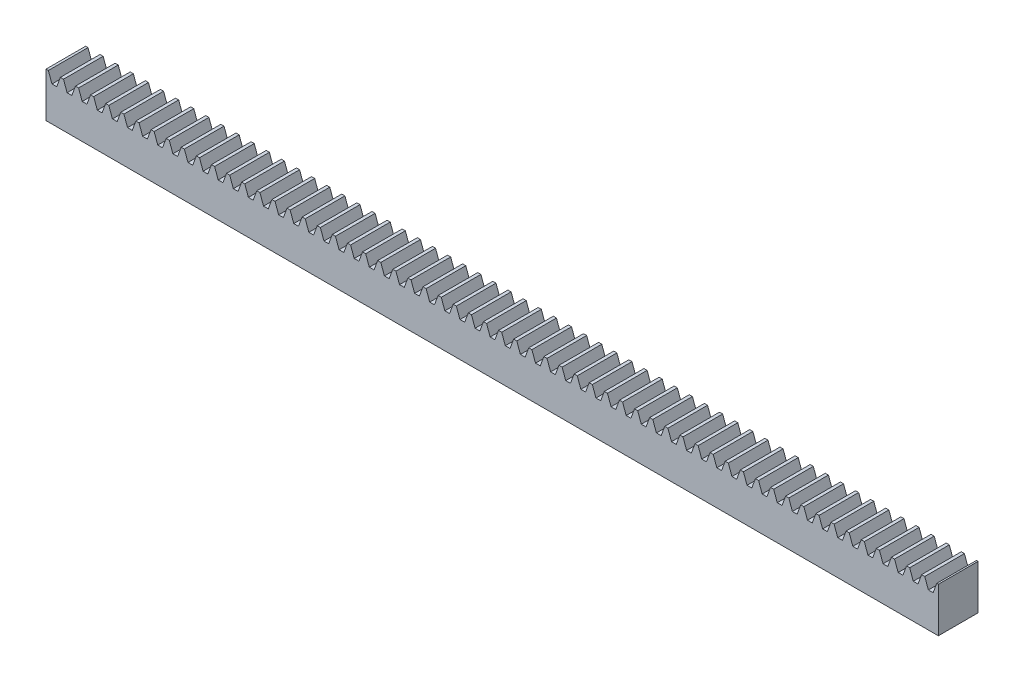
SolidWorks part; units mm, degrees
material "Nylon 101"
ref_plane "Front Plane" through (0, 0, 0) normal (0, 0, 1) x (1, 0, 0)
ref_plane "Top Plane" through (0, 0, 0) normal (0, 1, 0) x (1, 0, 0)
ref_plane "Right Plane" through (0, 0, 0) normal (1, 0, 0) x (0, 0, -1)
sketch "Sketch1" plane through (0, 0, 0) normal (0, 1, 0) x (1, 0, 0)
  line L0 (0, 0) -> (0, 4)
  line L1 (0, 4) -> (90, 4)
  line L2 (90, 4) -> (90, 0)
  line L3 (90, 0) -> (0, 0)
  dimension "D1" = 4
  dimension "D2" = 90
extrude "Boss-Extrude1" add sketch "Sketch1" along normal blind 4.5
sketch "Sketch2" plane through (0, 0, 0) normal (0, 0, 1) x (1, 0, 0)
  line L0 (0, 4) -> (90, 4) construction
  line L1 (0, 4.5) -> (0, 0) construction
  line L2 (90, 4.5) -> (90, 0) construction
  line L3 (0, 3.5) -> (90, 3.5) construction
  line L4 (0, 4.5) -> (90, 4.5) construction
  line L5 (0, 4.5) -> (0.239, 4.5) construction
  line L6 (0.239, 4.5) -> (0.603, 3.5)
  line L7 (0.603, 3.5) -> (0.842, 3.5)
  line L8 (1.081, 3.5) -> (1.445, 4.5)
  line L9 (1.445, 4.5) -> (1.684, 4.5) construction
  line L10 (0.842, 3.5) -> (1.081, 3.5)
  line L11 (0.239, 4.5) -> (1.445, 4.5)
  line L12 (1.763, 4.5) -> (2.127, 3.5)
  line L13 (2.127, 3.5) -> (2.366, 3.5)
  line L14 (2.605, 3.5) -> (2.969, 4.5)
  line L15 (2.366, 3.5) -> (2.605, 3.5)
  line L16 (1.763, 4.5) -> (2.969, 4.5)
  line L17 (1.524, 4.5) -> (1.763, 4.5) construction
  line L18 (2.969, 4.5) -> (3.208, 4.5) construction
  line L19 (3.287, 4.5) -> (3.651, 3.5)
  line L20 (3.651, 3.5) -> (3.89, 3.5)
  line L21 (4.129, 3.5) -> (4.493, 4.5)
  line L22 (3.89, 3.5) -> (4.129, 3.5)
  line L23 (3.287, 4.5) -> (4.493, 4.5)
  line L24 (3.048, 4.5) -> (3.287, 4.5) construction
  line L25 (4.493, 4.5) -> (4.732, 4.5) construction
  line L26 (4.811, 4.5) -> (5.175, 3.5)
  line L27 (5.175, 3.5) -> (5.414, 3.5)
  line L28 (5.653, 3.5) -> (6.017, 4.5)
  line L29 (5.414, 3.5) -> (5.653, 3.5)
  line L30 (4.811, 4.5) -> (6.017, 4.5)
  line L31 (4.572, 4.5) -> (4.811, 4.5) construction
  line L32 (6.017, 4.5) -> (6.256, 4.5) construction
  line L33 (6.335, 4.5) -> (6.699, 3.5)
  line L34 (6.699, 3.5) -> (6.938, 3.5)
  line L35 (7.177, 3.5) -> (7.541, 4.5)
  line L36 (6.938, 3.5) -> (7.177, 3.5)
  line L37 (6.335, 4.5) -> (7.541, 4.5)
  line L38 (6.096, 4.5) -> (6.335, 4.5) construction
  line L39 (7.541, 4.5) -> (7.78, 4.5) construction
  line L40 (7.859, 4.5) -> (8.223, 3.5)
  line L41 (8.223, 3.5) -> (8.462, 3.5)
  line L42 (8.701, 3.5) -> (9.065, 4.5)
  line L43 (8.462, 3.5) -> (8.701, 3.5)
  line L44 (7.859, 4.5) -> (9.065, 4.5)
  line L45 (7.62, 4.5) -> (7.859, 4.5) construction
  line L46 (9.065, 4.5) -> (9.304, 4.5) construction
  line L47 (9.383, 4.5) -> (9.747, 3.5)
  line L48 (9.747, 3.5) -> (9.986, 3.5)
  line L49 (10.225, 3.5) -> (10.589, 4.5)
  line L50 (9.986, 3.5) -> (10.225, 3.5)
  line L51 (9.383, 4.5) -> (10.589, 4.5)
  line L52 (9.144, 4.5) -> (9.383, 4.5) construction
  line L53 (10.589, 4.5) -> (10.828, 4.5) construction
  line L54 (10.907, 4.5) -> (11.271, 3.5)
  line L55 (11.271, 3.5) -> (11.51, 3.5)
  line L56 (11.749, 3.5) -> (12.113, 4.5)
  line L57 (11.51, 3.5) -> (11.749, 3.5)
  line L58 (10.907, 4.5) -> (12.113, 4.5)
  line L59 (10.668, 4.5) -> (10.907, 4.5) construction
  line L60 (12.113, 4.5) -> (12.352, 4.5) construction
  line L61 (12.431, 4.5) -> (12.795, 3.5)
  line L62 (12.795, 3.5) -> (13.034, 3.5)
  line L63 (13.273, 3.5) -> (13.637, 4.5)
  line L64 (13.034, 3.5) -> (13.273, 3.5)
  line L65 (12.431, 4.5) -> (13.637, 4.5)
  line L66 (12.192, 4.5) -> (12.431, 4.5) construction
  line L67 (13.637, 4.5) -> (13.876, 4.5) construction
  line L68 (13.955, 4.5) -> (14.319, 3.5)
  line L69 (14.319, 3.5) -> (14.558, 3.5)
  line L70 (14.797, 3.5) -> (15.161, 4.5)
  line L71 (14.558, 3.5) -> (14.797, 3.5)
  line L72 (13.955, 4.5) -> (15.161, 4.5)
  line L73 (13.716, 4.5) -> (13.955, 4.5) construction
  line L74 (15.161, 4.5) -> (15.4, 4.5) construction
  line L75 (15.479, 4.5) -> (15.843, 3.5)
  line L76 (15.843, 3.5) -> (16.082, 3.5)
  line L77 (16.321, 3.5) -> (16.685, 4.5)
  line L78 (16.082, 3.5) -> (16.321, 3.5)
  line L79 (15.479, 4.5) -> (16.685, 4.5)
  line L80 (15.24, 4.5) -> (15.479, 4.5) construction
  line L81 (16.685, 4.5) -> (16.924, 4.5) construction
  line L82 (17.003, 4.5) -> (17.367, 3.5)
  line L83 (17.367, 3.5) -> (17.606, 3.5)
  line L84 (17.845, 3.5) -> (18.209, 4.5)
  line L85 (17.606, 3.5) -> (17.845, 3.5)
  line L86 (17.003, 4.5) -> (18.209, 4.5)
  line L87 (16.764, 4.5) -> (17.003, 4.5) construction
  line L88 (18.209, 4.5) -> (18.448, 4.5) construction
  line L89 (18.527, 4.5) -> (18.891, 3.5)
  line L90 (18.891, 3.5) -> (19.13, 3.5)
  line L91 (19.369, 3.5) -> (19.733, 4.5)
  line L92 (19.13, 3.5) -> (19.369, 3.5)
  line L93 (18.527, 4.5) -> (19.733, 4.5)
  line L94 (18.288, 4.5) -> (18.527, 4.5) construction
  line L95 (19.733, 4.5) -> (19.972, 4.5) construction
  line L96 (20.051, 4.5) -> (20.415, 3.5)
  line L97 (20.415, 3.5) -> (20.654, 3.5)
  line L98 (20.893, 3.5) -> (21.257, 4.5)
  line L99 (20.654, 3.5) -> (20.893, 3.5)
  line L100 (20.051, 4.5) -> (21.257, 4.5)
  line L101 (19.812, 4.5) -> (20.051, 4.5) construction
  line L102 (21.257, 4.5) -> (21.496, 4.5) construction
  line L103 (21.575, 4.5) -> (21.939, 3.5)
  line L104 (21.939, 3.5) -> (22.178, 3.5)
  line L105 (22.417, 3.5) -> (22.781, 4.5)
  line L106 (22.178, 3.5) -> (22.417, 3.5)
  line L107 (21.575, 4.5) -> (22.781, 4.5)
  line L108 (21.336, 4.5) -> (21.575, 4.5) construction
  line L109 (22.781, 4.5) -> (23.02, 4.5) construction
  line L110 (23.099, 4.5) -> (23.463, 3.5)
  line L111 (23.463, 3.5) -> (23.702, 3.5)
  line L112 (23.941, 3.5) -> (24.305, 4.5)
  line L113 (23.702, 3.5) -> (23.941, 3.5)
  line L114 (23.099, 4.5) -> (24.305, 4.5)
  line L115 (22.86, 4.5) -> (23.099, 4.5) construction
  line L116 (24.305, 4.5) -> (24.544, 4.5) construction
  line L117 (24.623, 4.5) -> (24.987, 3.5)
  line L118 (24.987, 3.5) -> (25.226, 3.5)
  line L119 (25.465, 3.5) -> (25.829, 4.5)
  line L120 (25.226, 3.5) -> (25.465, 3.5)
  line L121 (24.623, 4.5) -> (25.829, 4.5)
  line L122 (24.384, 4.5) -> (24.623, 4.5) construction
  line L123 (25.829, 4.5) -> (26.068, 4.5) construction
  line L124 (26.147, 4.5) -> (26.511, 3.5)
  line L125 (26.511, 3.5) -> (26.75, 3.5)
  line L126 (26.989, 3.5) -> (27.353, 4.5)
  line L127 (26.75, 3.5) -> (26.989, 3.5)
  line L128 (26.147, 4.5) -> (27.353, 4.5)
  line L129 (25.908, 4.5) -> (26.147, 4.5) construction
  line L130 (27.353, 4.5) -> (27.592, 4.5) construction
  line L131 (27.671, 4.5) -> (28.035, 3.5)
  line L132 (28.035, 3.5) -> (28.274, 3.5)
  line L133 (28.513, 3.5) -> (28.877, 4.5)
  line L134 (28.274, 3.5) -> (28.513, 3.5)
  line L135 (27.671, 4.5) -> (28.877, 4.5)
  line L136 (27.432, 4.5) -> (27.671, 4.5) construction
  line L137 (28.877, 4.5) -> (29.116, 4.5) construction
  line L138 (29.195, 4.5) -> (29.559, 3.5)
  line L139 (29.559, 3.5) -> (29.798, 3.5)
  line L140 (30.037, 3.5) -> (30.401, 4.5)
  line L141 (29.798, 3.5) -> (30.037, 3.5)
  line L142 (29.195, 4.5) -> (30.401, 4.5)
  line L143 (28.956, 4.5) -> (29.195, 4.5) construction
  line L144 (30.401, 4.5) -> (30.64, 4.5) construction
  line L145 (30.719, 4.5) -> (31.083, 3.5)
  line L146 (31.083, 3.5) -> (31.322, 3.5)
  line L147 (31.561, 3.5) -> (31.925, 4.5)
  line L148 (31.322, 3.5) -> (31.561, 3.5)
  line L149 (30.719, 4.5) -> (31.925, 4.5)
  line L150 (30.48, 4.5) -> (30.719, 4.5) construction
  line L151 (31.925, 4.5) -> (32.164, 4.5) construction
  line L152 (32.243, 4.5) -> (32.607, 3.5)
  line L153 (32.607, 3.5) -> (32.846, 3.5)
  line L154 (33.085, 3.5) -> (33.449, 4.5)
  line L155 (32.846, 3.5) -> (33.085, 3.5)
  line L156 (32.243, 4.5) -> (33.449, 4.5)
  line L157 (32.004, 4.5) -> (32.243, 4.5) construction
  line L158 (33.449, 4.5) -> (33.688, 4.5) construction
  line L159 (33.767, 4.5) -> (34.131, 3.5)
  line L160 (34.131, 3.5) -> (34.37, 3.5)
  line L161 (34.609, 3.5) -> (34.973, 4.5)
  line L162 (34.37, 3.5) -> (34.609, 3.5)
  line L163 (33.767, 4.5) -> (34.973, 4.5)
  line L164 (33.528, 4.5) -> (33.767, 4.5) construction
  line L165 (34.973, 4.5) -> (35.212, 4.5) construction
  line L166 (35.291, 4.5) -> (35.655, 3.5)
  line L167 (35.655, 3.5) -> (35.894, 3.5)
  line L168 (36.133, 3.5) -> (36.497, 4.5)
  line L169 (35.894, 3.5) -> (36.133, 3.5)
  line L170 (35.291, 4.5) -> (36.497, 4.5)
  line L171 (35.052, 4.5) -> (35.291, 4.5) construction
  line L172 (36.497, 4.5) -> (36.736, 4.5) construction
  line L173 (36.815, 4.5) -> (37.179, 3.5)
  line L174 (37.179, 3.5) -> (37.418, 3.5)
  line L175 (37.657, 3.5) -> (38.021, 4.5)
  line L176 (37.418, 3.5) -> (37.657, 3.5)
  line L177 (36.815, 4.5) -> (38.021, 4.5)
  line L178 (36.576, 4.5) -> (36.815, 4.5) construction
  line L179 (38.021, 4.5) -> (38.26, 4.5) construction
  line L180 (38.339, 4.5) -> (38.703, 3.5)
  line L181 (38.703, 3.5) -> (38.942, 3.5)
  line L182 (39.181, 3.5) -> (39.545, 4.5)
  line L183 (38.942, 3.5) -> (39.181, 3.5)
  line L184 (38.339, 4.5) -> (39.545, 4.5)
  line L185 (38.1, 4.5) -> (38.339, 4.5) construction
  line L186 (39.545, 4.5) -> (39.784, 4.5) construction
  line L187 (39.863, 4.5) -> (40.227, 3.5)
  line L188 (40.227, 3.5) -> (40.466, 3.5)
  line L189 (40.705, 3.5) -> (41.069, 4.5)
  line L190 (40.466, 3.5) -> (40.705, 3.5)
  line L191 (39.863, 4.5) -> (41.069, 4.5)
  line L192 (39.624, 4.5) -> (39.863, 4.5) construction
  line L193 (41.069, 4.5) -> (41.308, 4.5) construction
  line L194 (41.387, 4.5) -> (41.751, 3.5)
  line L195 (41.751, 3.5) -> (41.99, 3.5)
  line L196 (42.229, 3.5) -> (42.593, 4.5)
  line L197 (41.99, 3.5) -> (42.229, 3.5)
  line L198 (41.387, 4.5) -> (42.593, 4.5)
  line L199 (41.148, 4.5) -> (41.387, 4.5) construction
  line L200 (42.593, 4.5) -> (42.832, 4.5) construction
  line L201 (42.911, 4.5) -> (43.275, 3.5)
  line L202 (43.275, 3.5) -> (43.514, 3.5)
  line L203 (43.753, 3.5) -> (44.117, 4.5)
  line L204 (43.514, 3.5) -> (43.753, 3.5)
  line L205 (42.911, 4.5) -> (44.117, 4.5)
  line L206 (42.672, 4.5) -> (42.911, 4.5) construction
  line L207 (44.117, 4.5) -> (44.356, 4.5) construction
  line L208 (44.435, 4.5) -> (44.799, 3.5)
  line L209 (44.799, 3.5) -> (45.038, 3.5)
  line L210 (45.277, 3.5) -> (45.641, 4.5)
  line L211 (45.038, 3.5) -> (45.277, 3.5)
  line L212 (44.435, 4.5) -> (45.641, 4.5)
  line L213 (44.196, 4.5) -> (44.435, 4.5) construction
  line L214 (45.641, 4.5) -> (45.88, 4.5) construction
  line L215 (45.959, 4.5) -> (46.323, 3.5)
  line L216 (46.323, 3.5) -> (46.562, 3.5)
  line L217 (46.801, 3.5) -> (47.165, 4.5)
  line L218 (46.562, 3.5) -> (46.801, 3.5)
  line L219 (45.959, 4.5) -> (47.165, 4.5)
  line L220 (45.72, 4.5) -> (45.959, 4.5) construction
  line L221 (47.165, 4.5) -> (47.404, 4.5) construction
  line L222 (47.483, 4.5) -> (47.847, 3.5)
  line L223 (47.847, 3.5) -> (48.086, 3.5)
  line L224 (48.325, 3.5) -> (48.689, 4.5)
  line L225 (48.086, 3.5) -> (48.325, 3.5)
  line L226 (47.483, 4.5) -> (48.689, 4.5)
  line L227 (47.244, 4.5) -> (47.483, 4.5) construction
  line L228 (48.689, 4.5) -> (48.928, 4.5) construction
  line L229 (49.007, 4.5) -> (49.371, 3.5)
  line L230 (49.371, 3.5) -> (49.61, 3.5)
  line L231 (49.849, 3.5) -> (50.213, 4.5)
  line L232 (49.61, 3.5) -> (49.849, 3.5)
  line L233 (49.007, 4.5) -> (50.213, 4.5)
  line L234 (48.768, 4.5) -> (49.007, 4.5) construction
  line L235 (50.213, 4.5) -> (50.452, 4.5) construction
  line L236 (50.531, 4.5) -> (50.895, 3.5)
  line L237 (50.895, 3.5) -> (51.134, 3.5)
  line L238 (51.373, 3.5) -> (51.737, 4.5)
  line L239 (51.134, 3.5) -> (51.373, 3.5)
  line L240 (50.531, 4.5) -> (51.737, 4.5)
  line L241 (50.292, 4.5) -> (50.531, 4.5) construction
  line L242 (51.737, 4.5) -> (51.976, 4.5) construction
  line L243 (52.055, 4.5) -> (52.419, 3.5)
  line L244 (52.419, 3.5) -> (52.658, 3.5)
  line L245 (52.897, 3.5) -> (53.261, 4.5)
  line L246 (52.658, 3.5) -> (52.897, 3.5)
  line L247 (52.055, 4.5) -> (53.261, 4.5)
  line L248 (51.816, 4.5) -> (52.055, 4.5) construction
  line L249 (53.261, 4.5) -> (53.5, 4.5) construction
  line L250 (53.579, 4.5) -> (53.943, 3.5)
  line L251 (53.943, 3.5) -> (54.182, 3.5)
  line L252 (54.421, 3.5) -> (54.785, 4.5)
  line L253 (54.182, 3.5) -> (54.421, 3.5)
  line L254 (53.579, 4.5) -> (54.785, 4.5)
  line L255 (53.34, 4.5) -> (53.579, 4.5) construction
  line L256 (54.785, 4.5) -> (55.024, 4.5) construction
  line L257 (55.103, 4.5) -> (55.467, 3.5)
  line L258 (55.467, 3.5) -> (55.706, 3.5)
  line L259 (55.945, 3.5) -> (56.309, 4.5)
  line L260 (55.706, 3.5) -> (55.945, 3.5)
  line L261 (55.103, 4.5) -> (56.309, 4.5)
  line L262 (54.864, 4.5) -> (55.103, 4.5) construction
  line L263 (56.309, 4.5) -> (56.548, 4.5) construction
  line L264 (56.627, 4.5) -> (56.991, 3.5)
  line L265 (56.991, 3.5) -> (57.23, 3.5)
  line L266 (57.469, 3.5) -> (57.833, 4.5)
  line L267 (57.23, 3.5) -> (57.469, 3.5)
  line L268 (56.627, 4.5) -> (57.833, 4.5)
  line L269 (56.388, 4.5) -> (56.627, 4.5) construction
  line L270 (57.833, 4.5) -> (58.072, 4.5) construction
  line L271 (58.151, 4.5) -> (58.515, 3.5)
  line L272 (58.515, 3.5) -> (58.754, 3.5)
  line L273 (58.993, 3.5) -> (59.357, 4.5)
  line L274 (58.754, 3.5) -> (58.993, 3.5)
  line L275 (58.151, 4.5) -> (59.357, 4.5)
  line L276 (57.912, 4.5) -> (58.151, 4.5) construction
  line L277 (59.357, 4.5) -> (59.596, 4.5) construction
  line L278 (59.675, 4.5) -> (60.039, 3.5)
  line L279 (60.039, 3.5) -> (60.278, 3.5)
  line L280 (60.517, 3.5) -> (60.881, 4.5)
  line L281 (60.278, 3.5) -> (60.517, 3.5)
  line L282 (59.675, 4.5) -> (60.881, 4.5)
  line L283 (59.436, 4.5) -> (59.675, 4.5) construction
  line L284 (60.881, 4.5) -> (61.12, 4.5) construction
  line L285 (61.199, 4.5) -> (61.563, 3.5)
  line L286 (61.563, 3.5) -> (61.802, 3.5)
  line L287 (62.041, 3.5) -> (62.405, 4.5)
  line L288 (61.802, 3.5) -> (62.041, 3.5)
  line L289 (61.199, 4.5) -> (62.405, 4.5)
  line L290 (60.96, 4.5) -> (61.199, 4.5) construction
  line L291 (62.405, 4.5) -> (62.644, 4.5) construction
  line L292 (62.723, 4.5) -> (63.087, 3.5)
  line L293 (63.087, 3.5) -> (63.326, 3.5)
  line L294 (63.565, 3.5) -> (63.929, 4.5)
  line L295 (63.326, 3.5) -> (63.565, 3.5)
  line L296 (62.723, 4.5) -> (63.929, 4.5)
  line L297 (62.484, 4.5) -> (62.723, 4.5) construction
  line L298 (63.929, 4.5) -> (64.168, 4.5) construction
  line L299 (64.247, 4.5) -> (64.611, 3.5)
  line L300 (64.611, 3.5) -> (64.85, 3.5)
  line L301 (65.089, 3.5) -> (65.453, 4.5)
  line L302 (64.85, 3.5) -> (65.089, 3.5)
  line L303 (64.247, 4.5) -> (65.453, 4.5)
  line L304 (64.008, 4.5) -> (64.247, 4.5) construction
  line L305 (65.453, 4.5) -> (65.692, 4.5) construction
  line L306 (65.771, 4.5) -> (66.135, 3.5)
  line L307 (66.135, 3.5) -> (66.374, 3.5)
  line L308 (66.613, 3.5) -> (66.977, 4.5)
  line L309 (66.374, 3.5) -> (66.613, 3.5)
  line L310 (65.771, 4.5) -> (66.977, 4.5)
  line L311 (65.532, 4.5) -> (65.771, 4.5) construction
  line L312 (66.977, 4.5) -> (67.216, 4.5) construction
  line L313 (67.295, 4.5) -> (67.659, 3.5)
  line L314 (67.659, 3.5) -> (67.898, 3.5)
  line L315 (68.137, 3.5) -> (68.501, 4.5)
  line L316 (67.898, 3.5) -> (68.137, 3.5)
  line L317 (67.295, 4.5) -> (68.501, 4.5)
  line L318 (67.056, 4.5) -> (67.295, 4.5) construction
  line L319 (68.501, 4.5) -> (68.74, 4.5) construction
  line L320 (68.819, 4.5) -> (69.183, 3.5)
  line L321 (69.183, 3.5) -> (69.422, 3.5)
  line L322 (69.661, 3.5) -> (70.025, 4.5)
  line L323 (69.422, 3.5) -> (69.661, 3.5)
  line L324 (68.819, 4.5) -> (70.025, 4.5)
  line L325 (68.58, 4.5) -> (68.819, 4.5) construction
  line L326 (70.025, 4.5) -> (70.264, 4.5) construction
  line L327 (70.343, 4.5) -> (70.707, 3.5)
  line L328 (70.707, 3.5) -> (70.946, 3.5)
  line L329 (71.185, 3.5) -> (71.549, 4.5)
  line L330 (70.946, 3.5) -> (71.185, 3.5)
  line L331 (70.343, 4.5) -> (71.549, 4.5)
  line L332 (70.104, 4.5) -> (70.343, 4.5) construction
  line L333 (71.549, 4.5) -> (71.788, 4.5) construction
  line L334 (71.867, 4.5) -> (72.231, 3.5)
  line L335 (72.231, 3.5) -> (72.47, 3.5)
  line L336 (72.709, 3.5) -> (73.073, 4.5)
  line L337 (72.47, 3.5) -> (72.709, 3.5)
  line L338 (71.867, 4.5) -> (73.073, 4.5)
  line L339 (71.628, 4.5) -> (71.867, 4.5) construction
  line L340 (73.073, 4.5) -> (73.312, 4.5) construction
  line L341 (73.391, 4.5) -> (73.755, 3.5)
  line L342 (73.755, 3.5) -> (73.994, 3.5)
  line L343 (74.233, 3.5) -> (74.597, 4.5)
  line L344 (73.994, 3.5) -> (74.233, 3.5)
  line L345 (73.391, 4.5) -> (74.597, 4.5)
  line L346 (73.152, 4.5) -> (73.391, 4.5) construction
  line L347 (74.597, 4.5) -> (74.836, 4.5) construction
  line L348 (74.915, 4.5) -> (75.279, 3.5)
  line L349 (75.279, 3.5) -> (75.518, 3.5)
  line L350 (75.757, 3.5) -> (76.121, 4.5)
  line L351 (75.518, 3.5) -> (75.757, 3.5)
  line L352 (74.915, 4.5) -> (76.121, 4.5)
  line L353 (74.676, 4.5) -> (74.915, 4.5) construction
  line L354 (76.121, 4.5) -> (76.36, 4.5) construction
  line L355 (76.439, 4.5) -> (76.803, 3.5)
  line L356 (76.803, 3.5) -> (77.042, 3.5)
  line L357 (77.281, 3.5) -> (77.645, 4.5)
  line L358 (77.042, 3.5) -> (77.281, 3.5)
  line L359 (76.439, 4.5) -> (77.645, 4.5)
  line L360 (76.2, 4.5) -> (76.439, 4.5) construction
  line L361 (77.645, 4.5) -> (77.884, 4.5) construction
  line L362 (77.963, 4.5) -> (78.327, 3.5)
  line L363 (78.327, 3.5) -> (78.566, 3.5)
  line L364 (78.805, 3.5) -> (79.169, 4.5)
  line L365 (78.566, 3.5) -> (78.805, 3.5)
  line L366 (77.963, 4.5) -> (79.169, 4.5)
  line L367 (77.724, 4.5) -> (77.963, 4.5) construction
  line L368 (79.169, 4.5) -> (79.408, 4.5) construction
  line L369 (79.487, 4.5) -> (79.851, 3.5)
  line L370 (79.851, 3.5) -> (80.09, 3.5)
  line L371 (80.329, 3.5) -> (80.693, 4.5)
  line L372 (80.09, 3.5) -> (80.329, 3.5)
  line L373 (79.487, 4.5) -> (80.693, 4.5)
  line L374 (79.248, 4.5) -> (79.487, 4.5) construction
  line L375 (80.693, 4.5) -> (80.932, 4.5) construction
  line L376 (81.011, 4.5) -> (81.375, 3.5)
  line L377 (81.375, 3.5) -> (81.614, 3.5)
  line L378 (81.853, 3.5) -> (82.217, 4.5)
  line L379 (81.614, 3.5) -> (81.853, 3.5)
  line L380 (81.011, 4.5) -> (82.217, 4.5)
  line L381 (80.772, 4.5) -> (81.011, 4.5) construction
  line L382 (82.217, 4.5) -> (82.456, 4.5) construction
  line L383 (82.535, 4.5) -> (82.899, 3.5)
  line L384 (82.899, 3.5) -> (83.138, 3.5)
  line L385 (83.377, 3.5) -> (83.741, 4.5)
  line L386 (83.138, 3.5) -> (83.377, 3.5)
  line L387 (82.535, 4.5) -> (83.741, 4.5)
  line L388 (82.296, 4.5) -> (82.535, 4.5) construction
  line L389 (83.741, 4.5) -> (83.98, 4.5) construction
  line L390 (84.059, 4.5) -> (84.423, 3.5)
  line L391 (84.423, 3.5) -> (84.662, 3.5)
  line L392 (84.901, 3.5) -> (85.265, 4.5)
  line L393 (84.662, 3.5) -> (84.901, 3.5)
  line L394 (84.059, 4.5) -> (85.265, 4.5)
  line L395 (83.82, 4.5) -> (84.059, 4.5) construction
  line L396 (85.265, 4.5) -> (85.504, 4.5) construction
  line L397 (85.583, 4.5) -> (85.947, 3.5)
  line L398 (85.947, 3.5) -> (86.186, 3.5)
  line L399 (86.425, 3.5) -> (86.789, 4.5)
  line L400 (86.186, 3.5) -> (86.425, 3.5)
  line L401 (85.583, 4.5) -> (86.789, 4.5)
  line L402 (85.344, 4.5) -> (85.583, 4.5) construction
  line L403 (86.789, 4.5) -> (87.028, 4.5) construction
  line L404 (87.107, 4.5) -> (87.471, 3.5)
  line L405 (87.471, 3.5) -> (87.71, 3.5)
  line L406 (87.949, 3.5) -> (88.313, 4.5)
  line L407 (87.71, 3.5) -> (87.949, 3.5)
  line L408 (87.107, 4.5) -> (88.313, 4.5)
  line L409 (86.868, 4.5) -> (87.107, 4.5) construction
  line L410 (88.313, 4.5) -> (88.552, 4.5) construction
  line L411 (88.631, 4.5) -> (88.995, 3.5)
  line L412 (88.995, 3.5) -> (89.234, 3.5)
  line L413 (89.473, 3.5) -> (89.837, 4.5)
  line L414 (89.234, 3.5) -> (89.473, 3.5)
  line L415 (88.631, 4.5) -> (89.837, 4.5)
  line L416 (88.392, 4.5) -> (88.631, 4.5) construction
  line L417 (89.837, 4.5) -> (90.076, 4.5) construction
  line L418 (90.155, 4.5) -> (90.519, 3.5)
  line L419 (90.519, 3.5) -> (90.758, 3.5)
  line L420 (90.997, 3.5) -> (91.361, 4.5)
  line L421 (90.758, 3.5) -> (90.997, 3.5)
  line L422 (90.155, 4.5) -> (91.361, 4.5)
  line L423 (89.916, 4.5) -> (90.155, 4.5) construction
  line L424 (91.361, 4.5) -> (91.6, 4.5) construction
  line L425 (91.679, 4.5) -> (92.043, 3.5)
  line L426 (92.043, 3.5) -> (92.282, 3.5)
  line L427 (92.521, 3.5) -> (92.885, 4.5)
  line L428 (92.282, 3.5) -> (92.521, 3.5)
  line L429 (91.679, 4.5) -> (92.885, 4.5)
  line L430 (91.44, 4.5) -> (91.679, 4.5) construction
  line L431 (92.885, 4.5) -> (93.124, 4.5) construction
  line L432 (93.203, 4.5) -> (93.567, 3.5)
  line L433 (93.567, 3.5) -> (93.806, 3.5)
  line L434 (94.045, 3.5) -> (94.409, 4.5)
  line L435 (93.806, 3.5) -> (94.045, 3.5)
  line L436 (93.203, 4.5) -> (94.409, 4.5)
  line L437 (92.964, 4.5) -> (93.203, 4.5) construction
  line L438 (94.409, 4.5) -> (94.648, 4.5) construction
  line L439 (94.727, 4.5) -> (95.091, 3.5)
  line L440 (95.091, 3.5) -> (95.33, 3.5)
  line L441 (95.569, 3.5) -> (95.933, 4.5)
  line L442 (95.33, 3.5) -> (95.569, 3.5)
  line L443 (94.727, 4.5) -> (95.933, 4.5)
  line L444 (94.488, 4.5) -> (94.727, 4.5) construction
  line L445 (95.933, 4.5) -> (96.172, 4.5) construction
  line L446 (96.251, 4.5) -> (96.615, 3.5)
  line L447 (96.615, 3.5) -> (96.854, 3.5)
  line L448 (97.093, 3.5) -> (97.457, 4.5)
  line L449 (96.854, 3.5) -> (97.093, 3.5)
  line L450 (96.251, 4.5) -> (97.457, 4.5)
  line L451 (96.012, 4.5) -> (96.251, 4.5) construction
  line L452 (97.457, 4.5) -> (97.696, 4.5) construction
  line L453 (97.775, 4.5) -> (98.139, 3.5)
  line L454 (98.139, 3.5) -> (98.378, 3.5)
  line L455 (98.617, 3.5) -> (98.981, 4.5)
  line L456 (98.378, 3.5) -> (98.617, 3.5)
  line L457 (97.775, 4.5) -> (98.981, 4.5)
  line L458 (97.536, 4.5) -> (97.775, 4.5) construction
  line L459 (98.981, 4.5) -> (99.22, 4.5) construction
  line L460 (99.299, 4.5) -> (99.663, 3.5)
  line L461 (99.663, 3.5) -> (99.902, 3.5)
  line L462 (100.141, 3.5) -> (100.505, 4.5)
  line L463 (99.902, 3.5) -> (100.141, 3.5)
  line L464 (99.299, 4.5) -> (100.505, 4.5)
  line L465 (99.06, 4.5) -> (99.299, 4.5) construction
  line L466 (100.505, 4.5) -> (100.744, 4.5) construction
  line L467 (100.823, 4.5) -> (101.187, 3.5)
  line L468 (101.187, 3.5) -> (101.426, 3.5)
  line L469 (101.665, 3.5) -> (102.029, 4.5)
  line L470 (101.426, 3.5) -> (101.665, 3.5)
  line L471 (100.823, 4.5) -> (102.029, 4.5)
  line L472 (100.584, 4.5) -> (100.823, 4.5) construction
  line L473 (102.029, 4.5) -> (102.268, 4.5) construction
  line L474 (102.347, 4.5) -> (102.711, 3.5)
  line L475 (102.711, 3.5) -> (102.95, 3.5)
  line L476 (103.189, 3.5) -> (103.553, 4.5)
  line L477 (102.95, 3.5) -> (103.189, 3.5)
  line L478 (102.347, 4.5) -> (103.553, 4.5)
  line L479 (102.108, 4.5) -> (102.347, 4.5) construction
  line L480 (103.553, 4.5) -> (103.792, 4.5) construction
  line L481 (103.871, 4.5) -> (104.235, 3.5)
  line L482 (104.235, 3.5) -> (104.474, 3.5)
  line L483 (104.713, 3.5) -> (105.077, 4.5)
  line L484 (104.474, 3.5) -> (104.713, 3.5)
  line L485 (103.871, 4.5) -> (105.077, 4.5)
  line L486 (103.632, 4.5) -> (103.871, 4.5) construction
  line L487 (105.077, 4.5) -> (105.316, 4.5) construction
  line L488 (105.395, 4.5) -> (105.759, 3.5)
  line L489 (105.759, 3.5) -> (105.998, 3.5)
  line L490 (106.237, 3.5) -> (106.601, 4.5)
  line L491 (105.998, 3.5) -> (106.237, 3.5)
  line L492 (105.395, 4.5) -> (106.601, 4.5)
  line L493 (105.156, 4.5) -> (105.395, 4.5) construction
  line L494 (106.601, 4.5) -> (106.84, 4.5) construction
  line L495 (106.919, 4.5) -> (107.283, 3.5)
  line L496 (107.283, 3.5) -> (107.522, 3.5)
  line L497 (107.761, 3.5) -> (108.125, 4.5)
  line L498 (107.522, 3.5) -> (107.761, 3.5)
  line L499 (106.919, 4.5) -> (108.125, 4.5)
  line L500 (106.68, 4.5) -> (106.919, 4.5) construction
  line L501 (108.125, 4.5) -> (108.364, 4.5) construction
  line L502 (108.443, 4.5) -> (108.807, 3.5)
  line L503 (108.807, 3.5) -> (109.046, 3.5)
  line L504 (109.285, 3.5) -> (109.649, 4.5)
  line L505 (109.046, 3.5) -> (109.285, 3.5)
  line L506 (108.443, 4.5) -> (109.649, 4.5)
  line L507 (108.204, 4.5) -> (108.443, 4.5) construction
  line L508 (109.649, 4.5) -> (109.888, 4.5) construction
  line L509 (109.967, 4.5) -> (110.331, 3.5)
  line L510 (110.331, 3.5) -> (110.57, 3.5)
  line L511 (110.809, 3.5) -> (111.173, 4.5)
  line L512 (110.57, 3.5) -> (110.809, 3.5)
  line L513 (109.967, 4.5) -> (111.173, 4.5)
  line L514 (109.728, 4.5) -> (109.967, 4.5) construction
  line L515 (111.173, 4.5) -> (111.412, 4.5) construction
  line L516 (111.491, 4.5) -> (111.855, 3.5)
  line L517 (111.855, 3.5) -> (112.094, 3.5)
  line L518 (112.333, 3.5) -> (112.697, 4.5)
  line L519 (112.094, 3.5) -> (112.333, 3.5)
  line L520 (111.491, 4.5) -> (112.697, 4.5)
  line L521 (111.252, 4.5) -> (111.491, 4.5) construction
  line L522 (112.697, 4.5) -> (112.936, 4.5) construction
  line L523 (113.015, 4.5) -> (113.379, 3.5)
  line L524 (113.379, 3.5) -> (113.618, 3.5)
  line L525 (113.857, 3.5) -> (114.221, 4.5)
  line L526 (113.618, 3.5) -> (113.857, 3.5)
  line L527 (113.015, 4.5) -> (114.221, 4.5)
  line L528 (112.776, 4.5) -> (113.015, 4.5) construction
  line L529 (114.221, 4.5) -> (114.46, 4.5) construction
  line L530 (114.539, 4.5) -> (114.903, 3.5)
  line L531 (114.903, 3.5) -> (115.142, 3.5)
  line L532 (115.381, 3.5) -> (115.745, 4.5)
  line L533 (115.142, 3.5) -> (115.381, 3.5)
  line L534 (114.539, 4.5) -> (115.745, 4.5)
  line L535 (114.3, 4.5) -> (114.539, 4.5) construction
  line L536 (115.745, 4.5) -> (115.984, 4.5) construction
  line L537 (116.063, 4.5) -> (116.427, 3.5)
  line L538 (116.427, 3.5) -> (116.666, 3.5)
  line L539 (116.905, 3.5) -> (117.269, 4.5)
  line L540 (116.666, 3.5) -> (116.905, 3.5)
  line L541 (116.063, 4.5) -> (117.269, 4.5)
  line L542 (115.824, 4.5) -> (116.063, 4.5) construction
  line L543 (117.269, 4.5) -> (117.508, 4.5) construction
  line L544 (117.587, 4.5) -> (117.951, 3.5)
  line L545 (117.951, 3.5) -> (118.19, 3.5)
  line L546 (118.429, 3.5) -> (118.793, 4.5)
  line L547 (118.19, 3.5) -> (118.429, 3.5)
  line L548 (117.587, 4.5) -> (118.793, 4.5)
  line L549 (117.348, 4.5) -> (117.587, 4.5) construction
  line L550 (118.793, 4.5) -> (119.032, 4.5) construction
  line L551 (119.111, 4.5) -> (119.475, 3.5)
  line L552 (119.475, 3.5) -> (119.714, 3.5)
  line L553 (119.953, 3.5) -> (120.317, 4.5)
  line L554 (119.714, 3.5) -> (119.953, 3.5)
  line L555 (119.111, 4.5) -> (120.317, 4.5)
  line L556 (118.872, 4.5) -> (119.111, 4.5) construction
  line L557 (120.317, 4.5) -> (120.556, 4.5) construction
  line L558 (120.635, 4.5) -> (120.999, 3.5)
  line L559 (120.999, 3.5) -> (121.238, 3.5)
  line L560 (121.477, 3.5) -> (121.841, 4.5)
  line L561 (121.238, 3.5) -> (121.477, 3.5)
  line L562 (120.635, 4.5) -> (121.841, 4.5)
  line L563 (120.396, 4.5) -> (120.635, 4.5) construction
  line L564 (121.841, 4.5) -> (122.08, 4.5) construction
  line L565 (122.159, 4.5) -> (122.523, 3.5)
  line L566 (122.523, 3.5) -> (122.762, 3.5)
  line L567 (123.001, 3.5) -> (123.365, 4.5)
  line L568 (122.762, 3.5) -> (123.001, 3.5)
  line L569 (122.159, 4.5) -> (123.365, 4.5)
  line L570 (121.92, 4.5) -> (122.159, 4.5) construction
  line L571 (123.365, 4.5) -> (123.604, 4.5) construction
  line L572 (123.683, 4.5) -> (124.047, 3.5)
  line L573 (124.047, 3.5) -> (124.286, 3.5)
  line L574 (124.525, 3.5) -> (124.889, 4.5)
  line L575 (124.286, 3.5) -> (124.525, 3.5)
  line L576 (123.683, 4.5) -> (124.889, 4.5)
  line L577 (123.444, 4.5) -> (123.683, 4.5) construction
  line L578 (124.889, 4.5) -> (125.128, 4.5) construction
  line L579 (125.207, 4.5) -> (125.571, 3.5)
  line L580 (125.571, 3.5) -> (125.81, 3.5)
  line L581 (126.049, 3.5) -> (126.413, 4.5)
  line L582 (125.81, 3.5) -> (126.049, 3.5)
  line L583 (125.207, 4.5) -> (126.413, 4.5)
  line L584 (124.968, 4.5) -> (125.207, 4.5) construction
  line L585 (126.413, 4.5) -> (126.652, 4.5) construction
  line L586 (126.731, 4.5) -> (127.095, 3.5)
  line L587 (127.095, 3.5) -> (127.334, 3.5)
  line L588 (127.573, 3.5) -> (127.937, 4.5)
  line L589 (127.334, 3.5) -> (127.573, 3.5)
  line L590 (126.731, 4.5) -> (127.937, 4.5)
  line L591 (126.492, 4.5) -> (126.731, 4.5) construction
  line L592 (127.937, 4.5) -> (128.176, 4.5) construction
  line L593 (128.255, 4.5) -> (128.619, 3.5)
  line L594 (128.619, 3.5) -> (128.858, 3.5)
  line L595 (129.097, 3.5) -> (129.461, 4.5)
  line L596 (128.858, 3.5) -> (129.097, 3.5)
  line L597 (128.255, 4.5) -> (129.461, 4.5)
  line L598 (128.016, 4.5) -> (128.255, 4.5) construction
  line L599 (129.461, 4.5) -> (129.7, 4.5) construction
  line L600 (129.779, 4.5) -> (130.143, 3.5)
  line L601 (130.143, 3.5) -> (130.382, 3.5)
  line L602 (130.621, 3.5) -> (130.985, 4.5)
  line L603 (130.382, 3.5) -> (130.621, 3.5)
  line L604 (129.779, 4.5) -> (130.985, 4.5)
  line L605 (129.54, 4.5) -> (129.779, 4.5) construction
  line L606 (130.985, 4.5) -> (131.224, 4.5) construction
  line L607 (131.303, 4.5) -> (131.667, 3.5)
  line L608 (131.667, 3.5) -> (131.906, 3.5)
  line L609 (132.145, 3.5) -> (132.509, 4.5)
  line L610 (131.906, 3.5) -> (132.145, 3.5)
  line L611 (131.303, 4.5) -> (132.509, 4.5)
  line L612 (131.064, 4.5) -> (131.303, 4.5) construction
  line L613 (132.509, 4.5) -> (132.748, 4.5) construction
  line L614 (132.827, 4.5) -> (133.191, 3.5)
  line L615 (133.191, 3.5) -> (133.43, 3.5)
  line L616 (133.669, 3.5) -> (134.033, 4.5)
  line L617 (133.43, 3.5) -> (133.669, 3.5)
  line L618 (132.827, 4.5) -> (134.033, 4.5)
  line L619 (132.588, 4.5) -> (132.827, 4.5) construction
  line L620 (134.033, 4.5) -> (134.272, 4.5) construction
  line L621 (134.351, 4.5) -> (134.715, 3.5)
  line L622 (134.715, 3.5) -> (134.954, 3.5)
  line L623 (135.193, 3.5) -> (135.557, 4.5)
  line L624 (134.954, 3.5) -> (135.193, 3.5)
  line L625 (134.351, 4.5) -> (135.557, 4.5)
  line L626 (134.112, 4.5) -> (134.351, 4.5) construction
  line L627 (135.557, 4.5) -> (135.796, 4.5) construction
  line L628 (135.875, 4.5) -> (136.239, 3.5)
  line L629 (136.239, 3.5) -> (136.478, 3.5)
  line L630 (136.717, 3.5) -> (137.081, 4.5)
  line L631 (136.478, 3.5) -> (136.717, 3.5)
  line L632 (135.875, 4.5) -> (137.081, 4.5)
  line L633 (135.636, 4.5) -> (135.875, 4.5) construction
  line L634 (137.081, 4.5) -> (137.32, 4.5) construction
  line L635 (137.399, 4.5) -> (137.763, 3.5)
  line L636 (137.763, 3.5) -> (138.002, 3.5)
  line L637 (138.241, 3.5) -> (138.605, 4.5)
  line L638 (138.002, 3.5) -> (138.241, 3.5)
  line L639 (137.399, 4.5) -> (138.605, 4.5)
  line L640 (137.16, 4.5) -> (137.399, 4.5) construction
  line L641 (138.605, 4.5) -> (138.844, 4.5) construction
  line L642 (138.923, 4.5) -> (139.287, 3.5)
  line L643 (139.287, 3.5) -> (139.526, 3.5)
  line L644 (139.765, 3.5) -> (140.129, 4.5)
  line L645 (139.526, 3.5) -> (139.765, 3.5)
  line L646 (138.923, 4.5) -> (140.129, 4.5)
  line L647 (138.684, 4.5) -> (138.923, 4.5) construction
  line L648 (140.129, 4.5) -> (140.368, 4.5) construction
  line L649 (140.447, 4.5) -> (140.811, 3.5)
  line L650 (140.811, 3.5) -> (141.05, 3.5)
  line L651 (141.289, 3.5) -> (141.653, 4.5)
  line L652 (141.05, 3.5) -> (141.289, 3.5)
  line L653 (140.447, 4.5) -> (141.653, 4.5)
  line L654 (140.208, 4.5) -> (140.447, 4.5) construction
  line L655 (141.653, 4.5) -> (141.892, 4.5) construction
  line L656 (141.971, 4.5) -> (142.335, 3.5)
  line L657 (142.335, 3.5) -> (142.574, 3.5)
  line L658 (142.813, 3.5) -> (143.177, 4.5)
  line L659 (142.574, 3.5) -> (142.813, 3.5)
  line L660 (141.971, 4.5) -> (143.177, 4.5)
  line L661 (141.732, 4.5) -> (141.971, 4.5) construction
  line L662 (143.177, 4.5) -> (143.416, 4.5) construction
  line L663 (143.495, 4.5) -> (143.859, 3.5)
  line L664 (143.859, 3.5) -> (144.098, 3.5)
  line L665 (144.337, 3.5) -> (144.701, 4.5)
  line L666 (144.098, 3.5) -> (144.337, 3.5)
  line L667 (143.495, 4.5) -> (144.701, 4.5)
  line L668 (143.256, 4.5) -> (143.495, 4.5) construction
  line L669 (144.701, 4.5) -> (144.94, 4.5) construction
  line L670 (145.019, 4.5) -> (145.383, 3.5)
  line L671 (145.383, 3.5) -> (145.622, 3.5)
  line L672 (145.861, 3.5) -> (146.225, 4.5)
  line L673 (145.622, 3.5) -> (145.861, 3.5)
  line L674 (145.019, 4.5) -> (146.225, 4.5)
  line L675 (144.78, 4.5) -> (145.019, 4.5) construction
  line L676 (146.225, 4.5) -> (146.464, 4.5) construction
  line L677 (146.543, 4.5) -> (146.907, 3.5)
  line L678 (146.907, 3.5) -> (147.146, 3.5)
  line L679 (147.385, 3.5) -> (147.749, 4.5)
  line L680 (147.146, 3.5) -> (147.385, 3.5)
  line L681 (146.543, 4.5) -> (147.749, 4.5)
  line L682 (146.304, 4.5) -> (146.543, 4.5) construction
  line L683 (147.749, 4.5) -> (147.988, 4.5) construction
  line L684 (148.067, 4.5) -> (148.431, 3.5)
  line L685 (148.431, 3.5) -> (148.67, 3.5)
  line L686 (148.909, 3.5) -> (149.273, 4.5)
  line L687 (148.67, 3.5) -> (148.909, 3.5)
  line L688 (148.067, 4.5) -> (149.273, 4.5)
  line L689 (147.828, 4.5) -> (148.067, 4.5) construction
  line L690 (149.273, 4.5) -> (149.512, 4.5) construction
  line L691 (149.591, 4.5) -> (149.955, 3.5)
  line L692 (149.955, 3.5) -> (150.194, 3.5)
  line L693 (150.433, 3.5) -> (150.797, 4.5)
  line L694 (150.194, 3.5) -> (150.433, 3.5)
  line L695 (149.591, 4.5) -> (150.797, 4.5)
  line L696 (149.352, 4.5) -> (149.591, 4.5) construction
  line L697 (150.797, 4.5) -> (151.036, 4.5) construction
  line L698 (151.115, 4.5) -> (151.479, 3.5)
  line L699 (151.479, 3.5) -> (151.718, 3.5)
  line L700 (151.957, 3.5) -> (152.321, 4.5)
  line L701 (151.718, 3.5) -> (151.957, 3.5)
  line L702 (151.115, 4.5) -> (152.321, 4.5)
  line L703 (150.876, 4.5) -> (151.115, 4.5) construction
  line L704 (152.321, 4.5) -> (152.56, 4.5) construction
  line L705 (152.639, 4.5) -> (153.003, 3.5)
  line L706 (153.003, 3.5) -> (153.242, 3.5)
  line L707 (153.481, 3.5) -> (153.845, 4.5)
  line L708 (153.242, 3.5) -> (153.481, 3.5)
  line L709 (152.639, 4.5) -> (153.845, 4.5)
  line L710 (152.4, 4.5) -> (152.639, 4.5) construction
  line L711 (153.845, 4.5) -> (154.084, 4.5) construction
  line L712 (154.163, 4.5) -> (154.527, 3.5)
  line L713 (154.527, 3.5) -> (154.766, 3.5)
  line L714 (155.005, 3.5) -> (155.369, 4.5)
  line L715 (154.766, 3.5) -> (155.005, 3.5)
  line L716 (154.163, 4.5) -> (155.369, 4.5)
  line L717 (153.924, 4.5) -> (154.163, 4.5) construction
  line L718 (155.369, 4.5) -> (155.608, 4.5) construction
  line L719 (155.687, 4.5) -> (156.051, 3.5)
  line L720 (156.051, 3.5) -> (156.29, 3.5)
  line L721 (156.529, 3.5) -> (156.893, 4.5)
  line L722 (156.29, 3.5) -> (156.529, 3.5)
  line L723 (155.687, 4.5) -> (156.893, 4.5)
  line L724 (155.448, 4.5) -> (155.687, 4.5) construction
  line L725 (156.893, 4.5) -> (157.132, 4.5) construction
  line L726 (157.211, 4.5) -> (157.575, 3.5)
  line L727 (157.575, 3.5) -> (157.814, 3.5)
  line L728 (158.053, 3.5) -> (158.417, 4.5)
  line L729 (157.814, 3.5) -> (158.053, 3.5)
  line L730 (157.211, 4.5) -> (158.417, 4.5)
  line L731 (156.972, 4.5) -> (157.211, 4.5) construction
  line L732 (158.417, 4.5) -> (158.656, 4.5) construction
  line L733 (158.735, 4.5) -> (159.099, 3.5)
  line L734 (159.099, 3.5) -> (159.338, 3.5)
  line L735 (159.577, 3.5) -> (159.941, 4.5)
  line L736 (159.338, 3.5) -> (159.577, 3.5)
  line L737 (158.735, 4.5) -> (159.941, 4.5)
  line L738 (158.496, 4.5) -> (158.735, 4.5) construction
  line L739 (159.941, 4.5) -> (160.18, 4.5) construction
  line L740 (160.259, 4.5) -> (160.623, 3.5)
  line L741 (160.623, 3.5) -> (160.862, 3.5)
  line L742 (161.101, 3.5) -> (161.465, 4.5)
  line L743 (160.862, 3.5) -> (161.101, 3.5)
  line L744 (160.259, 4.5) -> (161.465, 4.5)
  line L745 (160.02, 4.5) -> (160.259, 4.5) construction
  line L746 (161.465, 4.5) -> (161.704, 4.5) construction
  line L747 (161.783, 4.5) -> (162.147, 3.5)
  line L748 (162.147, 3.5) -> (162.386, 3.5)
  line L749 (162.625, 3.5) -> (162.989, 4.5)
  line L750 (162.386, 3.5) -> (162.625, 3.5)
  line L751 (161.783, 4.5) -> (162.989, 4.5)
  line L752 (161.544, 4.5) -> (161.783, 4.5) construction
  line L753 (162.989, 4.5) -> (163.228, 4.5) construction
  line L754 (163.307, 4.5) -> (163.671, 3.5)
  line L755 (163.671, 3.5) -> (163.91, 3.5)
  line L756 (164.149, 3.5) -> (164.513, 4.5)
  line L757 (163.91, 3.5) -> (164.149, 3.5)
  line L758 (163.307, 4.5) -> (164.513, 4.5)
  line L759 (163.068, 4.5) -> (163.307, 4.5) construction
  line L760 (164.513, 4.5) -> (164.752, 4.5) construction
  line L761 (164.831, 4.5) -> (165.195, 3.5)
  line L762 (165.195, 3.5) -> (165.434, 3.5)
  line L763 (165.673, 3.5) -> (166.037, 4.5)
  line L764 (165.434, 3.5) -> (165.673, 3.5)
  line L765 (164.831, 4.5) -> (166.037, 4.5)
  line L766 (164.592, 4.5) -> (164.831, 4.5) construction
  line L767 (166.037, 4.5) -> (166.276, 4.5) construction
  line L768 (166.355, 4.5) -> (166.719, 3.5)
  line L769 (166.719, 3.5) -> (166.958, 3.5)
  line L770 (167.197, 3.5) -> (167.561, 4.5)
  line L771 (166.958, 3.5) -> (167.197, 3.5)
  line L772 (166.355, 4.5) -> (167.561, 4.5)
  line L773 (166.116, 4.5) -> (166.355, 4.5) construction
  line L774 (167.561, 4.5) -> (167.8, 4.5) construction
  line L775 (167.879, 4.5) -> (168.243, 3.5)
  line L776 (168.243, 3.5) -> (168.482, 3.5)
  line L777 (168.721, 3.5) -> (169.085, 4.5)
  line L778 (168.482, 3.5) -> (168.721, 3.5)
  line L779 (167.879, 4.5) -> (169.085, 4.5)
  line L780 (167.64, 4.5) -> (167.879, 4.5) construction
  line L781 (169.085, 4.5) -> (169.324, 4.5) construction
  line L782 (169.403, 4.5) -> (169.767, 3.5)
  line L783 (169.767, 3.5) -> (170.006, 3.5)
  line L784 (170.245, 3.5) -> (170.609, 4.5)
  line L785 (170.006, 3.5) -> (170.245, 3.5)
  line L786 (169.403, 4.5) -> (170.609, 4.5)
  line L787 (169.164, 4.5) -> (169.403, 4.5) construction
  line L788 (170.609, 4.5) -> (170.848, 4.5) construction
  line L789 (170.927, 4.5) -> (171.291, 3.5)
  line L790 (171.291, 3.5) -> (171.53, 3.5)
  line L791 (171.769, 3.5) -> (172.133, 4.5)
  line L792 (171.53, 3.5) -> (171.769, 3.5)
  line L793 (170.927, 4.5) -> (172.133, 4.5)
  line L794 (170.688, 4.5) -> (170.927, 4.5) construction
  line L795 (172.133, 4.5) -> (172.372, 4.5) construction
  line L796 (172.451, 4.5) -> (172.815, 3.5)
  line L797 (172.815, 3.5) -> (173.054, 3.5)
  line L798 (173.293, 3.5) -> (173.657, 4.5)
  line L799 (173.054, 3.5) -> (173.293, 3.5)
  line L800 (172.451, 4.5) -> (173.657, 4.5)
  line L801 (172.212, 4.5) -> (172.451, 4.5) construction
  line L802 (173.657, 4.5) -> (173.896, 4.5) construction
  line L803 (173.975, 4.5) -> (174.339, 3.5)
  line L804 (174.339, 3.5) -> (174.578, 3.5)
  line L805 (174.817, 3.5) -> (175.181, 4.5)
  line L806 (174.578, 3.5) -> (174.817, 3.5)
  line L807 (173.975, 4.5) -> (175.181, 4.5)
  line L808 (173.736, 4.5) -> (173.975, 4.5) construction
  line L809 (175.181, 4.5) -> (175.42, 4.5) construction
  line L810 (175.499, 4.5) -> (175.863, 3.5)
  line L811 (175.863, 3.5) -> (176.102, 3.5)
  line L812 (176.341, 3.5) -> (176.705, 4.5)
  line L813 (176.102, 3.5) -> (176.341, 3.5)
  line L814 (175.499, 4.5) -> (176.705, 4.5)
  line L815 (175.26, 4.5) -> (175.499, 4.5) construction
  line L816 (176.705, 4.5) -> (176.944, 4.5) construction
  line L817 (177.023, 4.5) -> (177.387, 3.5)
  line L818 (177.387, 3.5) -> (177.626, 3.5)
  line L819 (177.865, 3.5) -> (178.229, 4.5)
  line L820 (177.626, 3.5) -> (177.865, 3.5)
  line L821 (177.023, 4.5) -> (178.229, 4.5)
  line L822 (176.784, 4.5) -> (177.023, 4.5) construction
  line L823 (178.229, 4.5) -> (178.468, 4.5) construction
  line L824 (178.547, 4.5) -> (178.911, 3.5)
  line L825 (178.911, 3.5) -> (179.15, 3.5)
  line L826 (179.389, 3.5) -> (179.753, 4.5)
  line L827 (179.15, 3.5) -> (179.389, 3.5)
  line L828 (178.547, 4.5) -> (179.753, 4.5)
  line L829 (178.308, 4.5) -> (178.547, 4.5) construction
  line L830 (179.753, 4.5) -> (179.992, 4.5) construction
  line L831 (180.071, 4.5) -> (180.435, 3.5)
  line L832 (180.435, 3.5) -> (180.674, 3.5)
  line L833 (180.913, 3.5) -> (181.277, 4.5)
  line L834 (180.674, 3.5) -> (180.913, 3.5)
  line L835 (180.071, 4.5) -> (181.277, 4.5)
  line L836 (179.832, 4.5) -> (180.071, 4.5) construction
  line L837 (181.277, 4.5) -> (181.516, 4.5) construction
  line L838 (181.595, 4.5) -> (181.959, 3.5)
  line L839 (181.959, 3.5) -> (182.198, 3.5)
  line L840 (182.437, 3.5) -> (182.801, 4.5)
  line L841 (182.198, 3.5) -> (182.437, 3.5)
  line L842 (181.595, 4.5) -> (182.801, 4.5)
  line L843 (181.356, 4.5) -> (181.595, 4.5) construction
  line L844 (182.801, 4.5) -> (183.04, 4.5) construction
  line L845 (183.119, 4.5) -> (183.483, 3.5)
  line L846 (183.483, 3.5) -> (183.722, 3.5)
  line L847 (183.961, 3.5) -> (184.325, 4.5)
  line L848 (183.722, 3.5) -> (183.961, 3.5)
  line L849 (183.119, 4.5) -> (184.325, 4.5)
  line L850 (182.88, 4.5) -> (183.119, 4.5) construction
  line L851 (184.325, 4.5) -> (184.564, 4.5) construction
  line L852 (184.643, 4.5) -> (185.007, 3.5)
  line L853 (185.007, 3.5) -> (185.246, 3.5)
  line L854 (185.485, 3.5) -> (185.849, 4.5)
  line L855 (185.246, 3.5) -> (185.485, 3.5)
  line L856 (184.643, 4.5) -> (185.849, 4.5)
  line L857 (184.404, 4.5) -> (184.643, 4.5) construction
  line L858 (185.849, 4.5) -> (186.088, 4.5) construction
  line L859 (186.167, 4.5) -> (186.531, 3.5)
  line L860 (186.531, 3.5) -> (186.77, 3.5)
  line L861 (187.009, 3.5) -> (187.373, 4.5)
  line L862 (186.77, 3.5) -> (187.009, 3.5)
  line L863 (186.167, 4.5) -> (187.373, 4.5)
  line L864 (185.928, 4.5) -> (186.167, 4.5) construction
  line L865 (187.373, 4.5) -> (187.612, 4.5) construction
  line L866 (187.691, 4.5) -> (188.055, 3.5)
  line L867 (188.055, 3.5) -> (188.294, 3.5)
  line L868 (188.533, 3.5) -> (188.897, 4.5)
  line L869 (188.294, 3.5) -> (188.533, 3.5)
  line L870 (187.691, 4.5) -> (188.897, 4.5)
  line L871 (187.452, 4.5) -> (187.691, 4.5) construction
  line L872 (188.897, 4.5) -> (189.136, 4.5) construction
  line L873 (189.215, 4.5) -> (189.579, 3.5)
  line L874 (189.579, 3.5) -> (189.818, 3.5)
  line L875 (190.057, 3.5) -> (190.421, 4.5)
  line L876 (189.818, 3.5) -> (190.057, 3.5)
  line L877 (189.215, 4.5) -> (190.421, 4.5)
  line L878 (188.976, 4.5) -> (189.215, 4.5) construction
  line L879 (190.421, 4.5) -> (190.66, 4.5) construction
  dimension "D1" = 0.5
  dimension "D2" = 0.5
  dimension "D3" = 110
  dimension "D4" = 0.842
  dimension "D5" = 125
extrude "Cut-Extrude1" cut sketch "Sketch2" against normal through all
